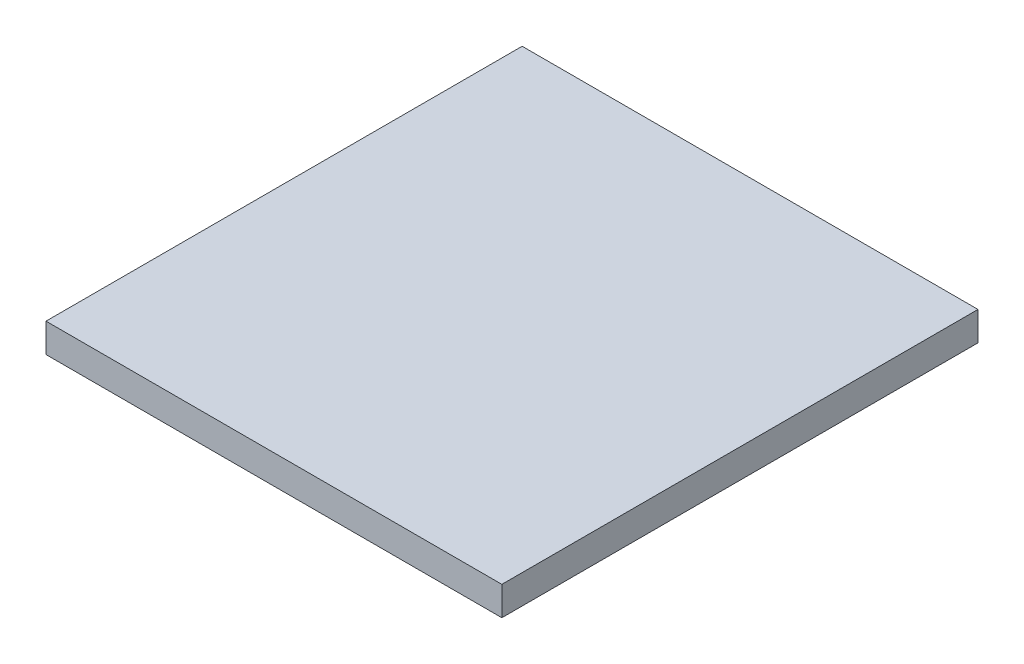
SolidWorks part; units mm, degrees
ref_plane "Front Plane" through (0, 0, 0) normal (0, 0, 1) x (1, 0, 0)
ref_plane "Top Plane" through (0, 0, 0) normal (0, 1, 0) x (1, 0, 0)
ref_plane "Right Plane" through (0, 0, 0) normal (1, 0, 0) x (0, 0, -1)
sketch "Sketch1" plane through (0, 0, 0) normal (0, 1, 0) x (1, 0, 0)
  line L1 (-300, 313.355) -> (300, 313.355)
  line L2 (-300, 313.355) -> (-300, -313.355)
  line L3 (-300, -313.355) -> (300, -313.355)
  line L5 (-300, 313.355) -> (300, -313.355) construction
  line L6 (300, -313.355) -> (300, 313.355)
  point P0 (0, 0)
  point P4 (357.5812, 294.305)
  dimension "D1" = 626.71
  dimension "D2" = 600
extrude "Boss-Extrude1" add sketch "Sketch1" along normal blind 38.1
